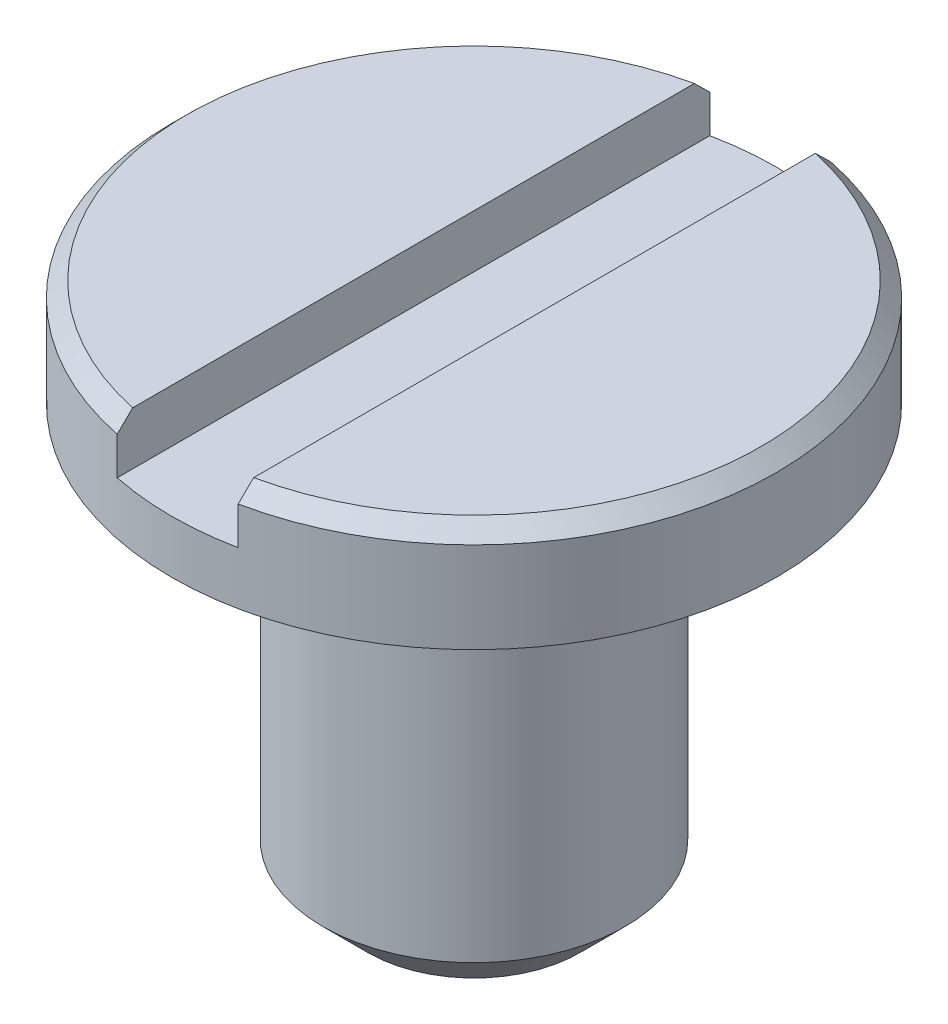
SolidWorks part; units mm, degrees
ref_plane "Alzado" through (0, 0, 0) normal (0, 0, 1) x (1, 0, 0)
ref_plane "Planta" through (0, 0, 0) normal (0, 1, 0) x (1, 0, 0)
ref_plane "Vista lateral" through (0, 0, 0) normal (1, 0, 0) x (0, 0, -1)
sketch "Sketch1" plane through (0, 0, 0) normal (0, 1, 0) x (1, 0, 0)
  circle A0 centre (0, 0) radius 1
  dimension "D1" = 2
extrude "Boss-Extrude1" add sketch "Sketch1" along normal blind 0.35
sketch "Sketch2" plane through (0, 0, 0) normal (0, 1, 0) x (1, 0, 0)
  circle A0 centre (0, 0) radius 0.5
  dimension "D1" = 1
extrude "Boss-Extrude2" add sketch "Sketch2" against normal blind 1.4
chamfer "Chamfer1" distance 0.05 angle 45 1 edges at (0, 0.35, 1)
chamfer "Chamfer2" distance 0.15 angle 45 1 edges at (0, -1.4, 0.5)
sketch "Sketch3" plane through (0, 0, 0) normal (0, 0, 1) x (1, 0, 0)
  line L0 (0, -1000) -> (0, 49000) construction
  line L1 (0.95, 0.35) -> (-0.95, 0.35) construction
  line L2 (-0.2, -999.9073) -> (-0.2, 49000.0927) construction
  line L3 (0.95, 0.35) -> (-0.95, 0.35) construction
  line L4 (-1000.8273, 0.175) -> (48999.1727, 0.175) construction
  line L5 (-0.2, 0.35) -> (0, 0.35)
  line L6 (-0.2, 0.35) -> (-0.2, 0.175)
  line L7 (0.2, 0.175) -> (0, 0.175)
  line L8 (-0.2, 0.175) -> (0, 0.175)
  line L9 (0.2, 0.35) -> (0.2, 0.175)
  line L10 (0.2, 0.35) -> (0, 0.35)
  dimension "D1" = 0.175
  dimension "D2" = 0.2
extrude "Cut-Extrude1" cut sketch "Sketch3" against normal through all both and the other way through all
